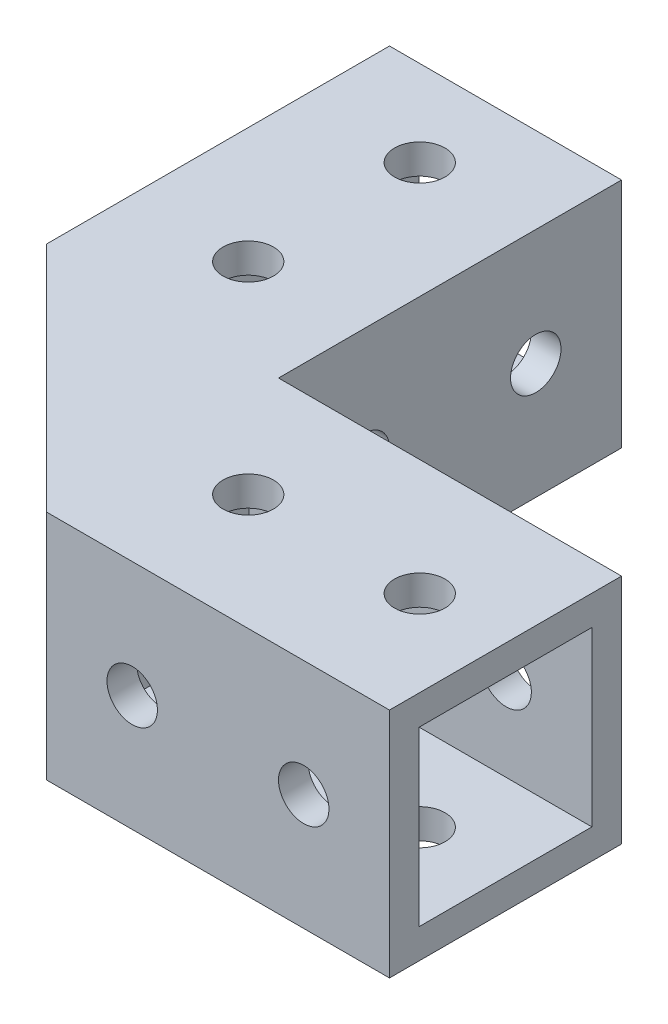
SolidWorks part; units mm, degrees
ref_plane "Front Plane" through (0, 0, 0) normal (0, 0, 1) x (1, 0, 0)
ref_plane "Top Plane" through (0, 0, 0) normal (0, 1, 0) x (1, 0, 0)
ref_plane "Right Plane" through (0, 0, 0) normal (1, 0, 0) x (0, 0, -1)
other "Configuration Table"
sketch "sketch1" plane through (0, 0, 0) normal (0, 1, 0) x (1, 0, 0)
  line L0 (0, -11.5) -> (8.5, -11.5) construction
  line L1 (0, 0) -> (34, 0)
  line L2 (0, 0) -> (0, -23)
  line L3 (0, -23) -> (34, -23)
  line L4 (34, 0) -> (34, -23)
  line L5 (8.5, -11.5) -> (25.5, -11.5) construction
  circle A1 centre (8.5, -11.5) radius 2.5
  circle A2 centre (25.5, -11.5) radius 2.5
  dimension "D4" = 5
  dimension "D1" = 23
  dimension "D2" = 34
  dimension "D3" = 8.5
  dimension "D6" = 17
  dimension "D5" = 2
extrude "Boss-Extrude1" add sketch "sketch1" along normal blind 23
sketch "Sketch6" plane through (0, 0, 0) normal (0, 0, -1) x (-1, 0, 0)
  line L0 (-34, 11.5) -> (-25.5, 11.5) construction
  line L1 (-25.5, 11.5) -> (-8.5, 11.5) construction
  line L4 (-34, 0) -> (0, 0)
  line L5 (0, 0) -> (0, 23)
  line L6 (0, 23) -> (-34, 23)
  line L7 (-34, 23) -> (-34, 0)
  line L8 (-34, 0) -> (0, 0)
  line L9 (0, 0) -> (0, 23)
  line L10 (0, 23) -> (-34, 23)
  line L11 (-34, 23) -> (-34, 0)
  circle A0 centre (-25.5, 11.5) radius 2.5
  circle A1 centre (-8.5, 11.5) radius 2.5
  dimension "D3" = 5
  dimension "D2" = 8.5
  dimension "D5" = 17
  dimension "D4" = 2
extrude "Cut-Extrude10" cut sketch "Sketch6" against normal through all flip side to cut
sketch "Sketch7" plane through (34, 0, 0) normal (1, 0, 0) x (0, 0, -1)
  line L0 (-23, 11.5) -> (0, 11.5) construction
  line L4 (-23, 0) -> (0, 0)
  line L5 (0, 0) -> (0, 23)
  line L6 (0, 23) -> (-23, 23)
  line L7 (-23, 23) -> (-23, 0)
  line L8 (-23, 0) -> (0, 0)
  line L9 (0, 0) -> (0, 23)
  line L10 (0, 23) -> (-23, 23)
  line L11 (-23, 23) -> (-23, 0)
  line L14 (-20.06, 20.06) -> (-2.94, 20.06)
  line L15 (-20.06, 20.06) -> (-20.06, 2.94)
  line L16 (-20.06, 2.94) -> (-2.94, 2.94)
  line L17 (-2.94, 20.06) -> (-2.94, 2.94)
  line L18 (-20.06, 20.06) -> (-2.94, 2.94) construction
  line L19 (-20.06, 2.94) -> (-2.94, 20.06) construction
  point P6 (-11.5, 11.5)
  dimension "D2" = 17.12
extrude "Cut-Extrude11" cut sketch "Sketch7" against normal blind 34 flip side to cut
sketch "Sketch9" plane through (0, 0, 0) normal (0, 1, 0) x (1, 0, 0)
  line L0 (0, 0) -> (34, 0) construction
  line L1 (0, 0) -> (24.0416, 24.0416) construction
  dimension "D1" = 45
ref_plane "Plane2" through (0, 0, 0) normal (-0.7071, 0, -0.7071) x (-0.7071, 0, 0.7071)
mirror "Mirror6" about plane through (0, 0, 0) normal (-0.7071, 0, -0.7071) of bodies 118 110
sketch "Sketch11" plane through (0, 0, 0) normal (0, 1, 0) x (1, 0, 0)
  line L0 (-23, 0) -> (0, -23)
  line L1 (0, 0) -> (-23, 0) construction
  line L2 (0, 0) -> (0, -23) construction
  line L3 (0, 0) -> (-23, 0)
  line L4 (0, 0) -> (0, -23)
extrude "Boss-Extrude2" add sketch "Sketch11" along normal blind 23
sketch "Sketch13" plane through (0, 0, 0) normal (0, 1, 0) x (1, 0, 0)
  line L0 (-11.5, 8.5) -> (5.1708, 5.1708) construction
  line L1 (0, 0) -> (24.0416, 24.0416) construction
  line L2 (5.1708, 5.1708) -> (8.5, -11.5) construction
  line L4 (8.7064, 8.7064) -> (0, 17)
  line L5 (0, 34) -> (0, 0) construction
  line L6 (8.7064, 8.7064) -> (17, 0)
  line L7 (0, 0) -> (34, 0) construction
  line L8 (0, 0) -> (24.0416, 24.0416) construction
  line L9 (0, 17) -> (0, 0)
  line L10 (0, 0) -> (17, 0)
  circle A0 centre (8.5, -11.5) radius 2.5 construction
  circle A1 centre (-11.5, 8.5) radius 2.5 construction
  circle A2 centre (8.5, -11.5) radius 2.5 construction
  circle A3 centre (-11.5, 8.5) radius 2.5 construction
  circle A4 centre (5.1708, 5.1708) radius 2.5
  dimension "D3" = 5
  dimension "D2" = 5
  dimension "D1" = 17
  dimension "D4" = 17
extrude "Boss-Extrude3" add sketch "Sketch13" along normal blind 4
equation "\"D2@sketch1\" = \"length\""
equation "\"holes\"= 2'Holes per side"
equation "\"cdist\"= 17mm'centre distance between holes"
equation "\"width\"= \"insetwidth\" + 2 * \"shellwidth\""
equation "\"length\"= \"cdist\" * \"holes\""
equation "\"D1@sketch1\"=\"width\""
equation "\"hdiam\"= 5mm'Hole diametre"
equation "\"D4@sketch1\" = \"hdiam\""
equation "\"D6@sketch1\" = \"cdist\""
equation "\"D5@sketch1\" = \"holes\""
equation "\"D2@Sketch6\"=\"cdist\"/2"
equation "\"D3@Sketch6\"=\"hdiam\""
equation "\"D5@Sketch6\"=\"cdist\""
equation "\"D4@Sketch6\"=\"holes\""
equation "\"D1@Boss-Extrude1\"=\"width\""
equation "\"joint\"= 90"
equation "\"D1@Sketch9\"=\"joint\"/2"
equation "\"D1@Boss-Extrude2\"=\"width\""
equation "\"D2@Sketch13\"=\"hdiam\""
equation "\"D4@Sketch13\"=\"cdist\""
equation "\"D1@Boss-Extrude3\"=\"supportheight\""
equation "\"supportheight\"= 4mm"
equation "\"tolerance\"= 0.06mm"
equation "\"insetwidth\"= 17mm"
equation "\"D1@Cut-Extrude11\"=\"length\""
equation "\"true\"= 1"
equation "\"false\"= 0"
equation "\"supportenabled\"= \"true\""
equation "\"Boss-Extrude3\"= IIF ( \"supportenabled\" < \"true\" , \"suppressed\" , \"unsuppressed\" )"
equation "\"D2@Sketch7\"=\"insetwidth\"+\"tolerance\"*2"
equation "\"shellwidth\"= 3mm"
